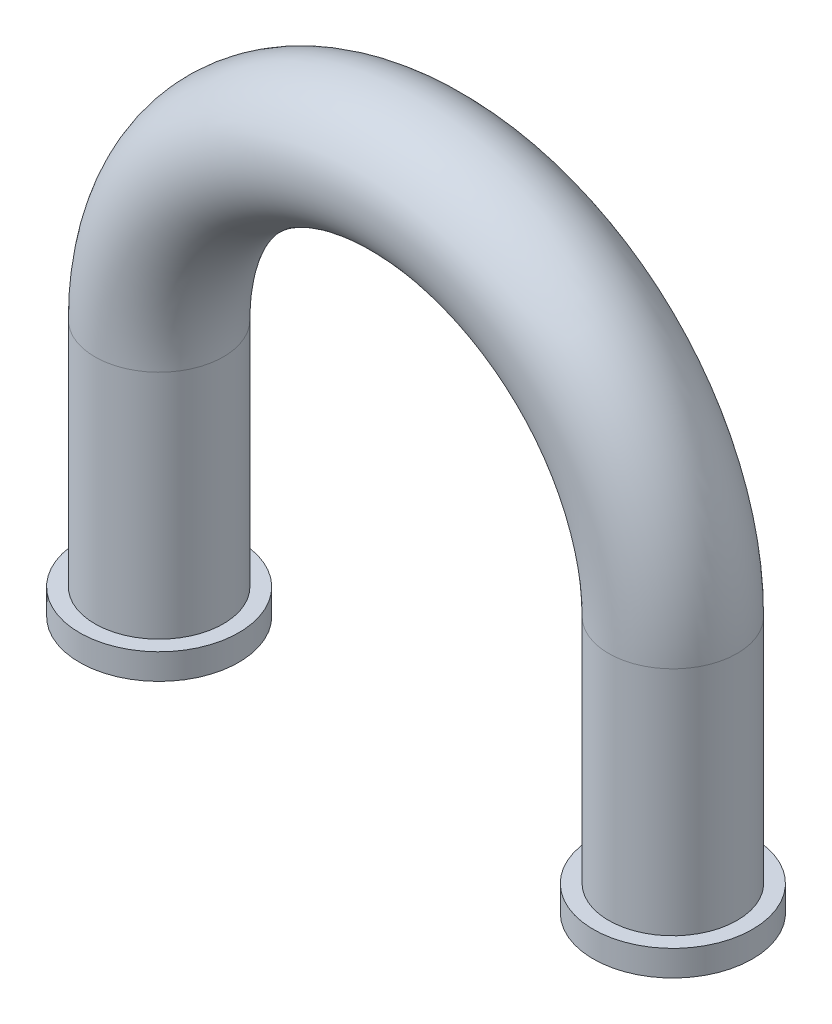
SolidWorks part; units mm, degrees
ref_plane "Ön Düzlem" through (0, 0, 0) normal (0, 0, 1) x (1, 0, 0)
ref_plane "Üst Düzlem" through (0, 0, 0) normal (0, 1, 0) x (1, 0, 0)
ref_plane "Sağ Düzlem" through (0, 0, 0) normal (1, 0, 0) x (0, 0, -1)
sketch "Çizim1" plane through (0, 0, 0) normal (0, 0, 1) x (1, 0, 0)
  line L0 (1, 0) -> (1, -1)
  arc A0 (0, 1) -> (1, 0) centre (0, 0) cw
sketch "Çizim3" plane through (0, 0, 0) normal (1, 0, 0) x (0, 0, -1)
  line L0 (0, 1) -> (0, 0) construction
  circle A0 centre (0, 1) radius 0.2
sweep "Süpür-İnce1" add profiles "Çizim3" path "Çizim1" parameters "D1"=0.05
ref_plane "Düzlem1" through (0, -1, 0) normal (0, -1, 0) x (-1, 0, 0)
sketch "Çizim5" plane through (0, -1, 0) normal (0, -1, 0) x (-1, 0, 0)
  circle A0 centre (-1, 0) radius 0.21
sketch "Çizim6" plane through (0, 0, 0) normal (0, 0, 1) x (1, 0, 0)
  line L0 (1, -1) -> (1, -0.9)
  line L1 (0.79, -1) -> (1.21, -1) construction
sweep "Süpür-İnce3" add profiles "Çizim5" path "Çizim6" parameters "D1"=0.1
mirror "Aynalama1" about plane through (0, 0, 0) normal (1, 0, 0) of bodies 103
